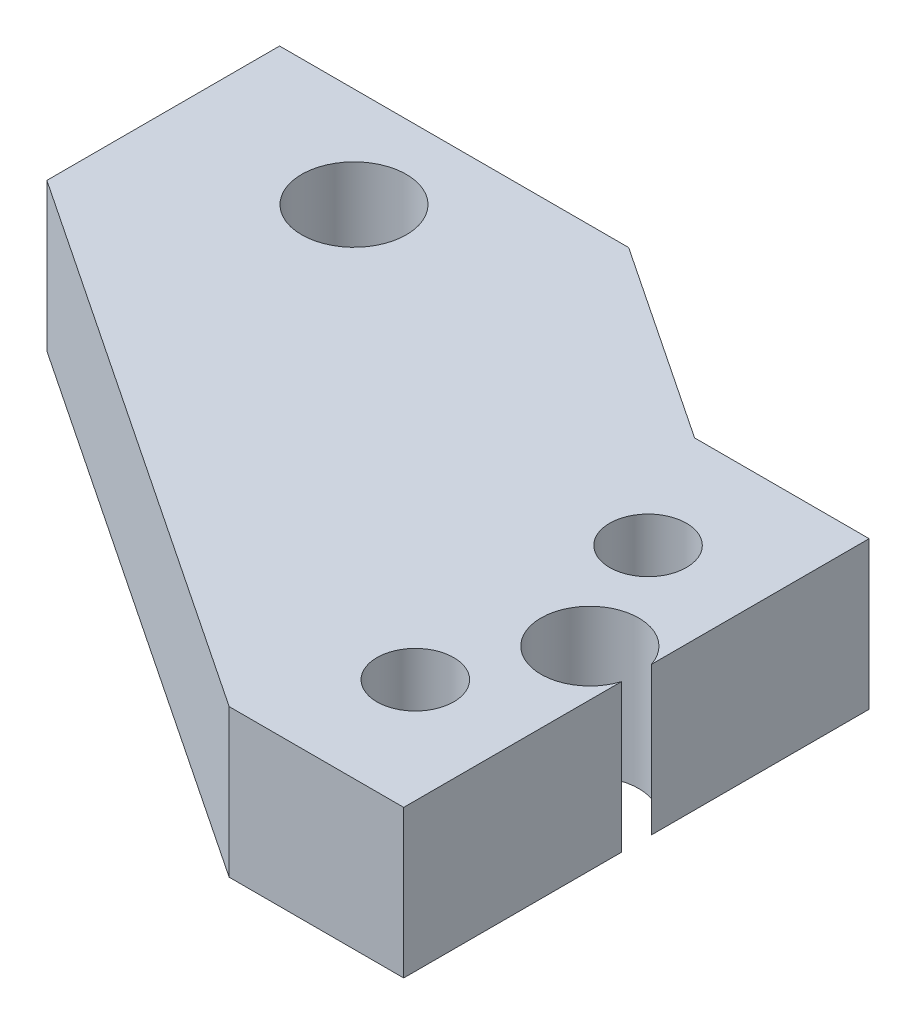
SolidWorks part; units mm, degrees
material "6061-T6 (SS)"
ref_plane "Front Plane" through (0, 0, 0) normal (0, 0, 1) x (1, 0, 0)
ref_plane "Top Plane" through (0, 0, 0) normal (0, 1, 0) x (1, 0, 0)
ref_plane "Right Plane" through (0, 0, 0) normal (1, 0, 0) x (0, 0, -1)
sketch "Sketch1" plane through (0, 0, 0) normal (0, 1, 0) x (1, 0, 0)
  line L0 (0, 0) -> (0, 20)
  line L1 (0, 20) -> (-7.5, 20)
  line L2 (-7.5, 20) -> (-16, 25.6667)
  line L3 (-16, 25.6667) -> (-31, 25.6667)
  line L4 (-31, 25.6667) -> (-31, 15.6667)
  line L5 (-31, 15.6667) -> (-7.5, 0)
  line L6 (-7.5, 0) -> (0, 0)
  dimension "D1" = 20
  dimension "D2" = 7.5
  dimension "D3" = 7.5
  dimension "D4" = 31
  dimension "D5" = 10
  dimension "D6" = 15
extrude "Boss-Extrude1" add sketch "Sketch1" along normal mid plane 6.35
hole_wizard "M4 Clearance Hole1" positions "Sketch2" profile "Sketch3" hole size "M4" standard "ANSI Metric" end condition through all
sketch "Sketch2" plane through (0, 3.175, 0) normal (0, 1, 0) x (1, 0, 0)
  point P0 (-23.5, 21.3645)
sketch "Sketch3" plane through (-23.5, 3.175, -21.3645) normal (1, 0, 0) x (0, 0, 1)
  line L0 (0, 0) -> (0, 6.35)
  line L1 (0, 6.35) -> (2.25, 6.35)
  line L2 (2.25, 6.35) -> (2.25, 0)
  line L5 (2.25, 0) -> (0, 0)
  line L11 (0, -6.35) -> (0, 107.95) construction
  dimension "Thru Hole Dia." = 4.5
  dimension "Thru Hole Depth" = 6.35
hole_wizard "M4x0.7 Tapped Hole1" positions "Sketch4" profile "Sketch6" tap size "M4x0.7" standard "ANSI Metric" end condition through all
sketch "Sketch4" plane through (0, 3.175, 0) normal (0, 1, 0) x (1, 0, 0)
  point P10 (-4.5, 15)
  point P13 (-4.5, 5)
sketch "Sketch6" plane through (-4.5, 3.175, -15) normal (1, 0, 0) x (0, 0, 1)
  line L0 (0, 0) -> (0, 6.35)
  line L1 (0, 6.35) -> (1.65, 6.35)
  line L2 (1.65, 6.35) -> (1.65, 0)
  line L5 (1.65, 0) -> (0, 0)
  line L11 (0, -6.35) -> (0, 107.95) construction
  dimension "Thru Tap Drill Dia." = 3.3
  dimension "Thru Tap Drill Depth" = 6.35
cosmetic thread "Hole Thread1" parameters "D2"=4
cosmetic thread "Hole Thread2" parameters "D2"=4
hole_wizard "M5x0.8 Tapped Hole1" positions "Sketch7" profile "Sketch8" tap size "M5x0.8" standard "ANSI Metric" end condition through all
sketch "Sketch7" plane through (0, 3.175, 0) normal (0, 1, 0) x (1, 0, 0)
  point P0 (-2, 10)
sketch "Sketch8" plane through (-2, 3.175, -10) normal (1, 0, 0) x (0, 0, 1)
  line L0 (0, 0) -> (0, 6.35)
  line L1 (0, 6.35) -> (2.1, 6.35)
  line L2 (2.1, 6.35) -> (2.1, 0)
  line L5 (2.1, 0) -> (0, 0)
  line L11 (0, -6.35) -> (0, 107.95) construction
  dimension "Thru Tap Drill Dia." = 4.2
  dimension "Thru Tap Drill Depth" = 6.35
cosmetic thread "Hole Thread3" parameters "D2"=5
